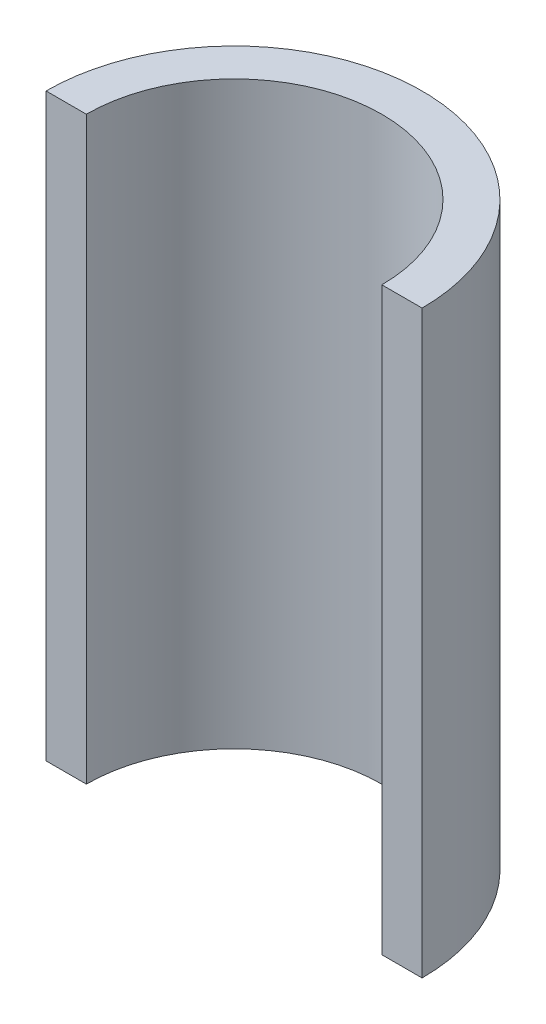
SolidWorks part; units mm, degrees
ref_plane "Plan de face" through (0, 0, 0) normal (0, 0, 1) x (1, 0, 0)
ref_plane "Plan de dessus" through (0, 0, 0) normal (0, 1, 0) x (1, 0, 0)
ref_plane "Plan de droite" through (0, 0, 0) normal (1, 0, 0) x (0, 0, -1)
sketch "Esquisse1" plane through (0, 0, 0) normal (0, 1, 0) x (1, 0, 0)
  line L0 (17.6, 0) -> (22.4, 0)
  line L1 (-17.6, 0) -> (-22.4, 0)
  arc A0 (22.4, 0) -> (-22.4, 0) centre (0, 0) ccw
  arc A1 (17.6, 0) -> (-17.6, 0) centre (0, 0) ccw
  dimension "D1" = 35.2
  dimension "D2" = 44.8
extrude "Boss.-Extru.1" add sketch "Esquisse1" along normal mid plane 69.12
